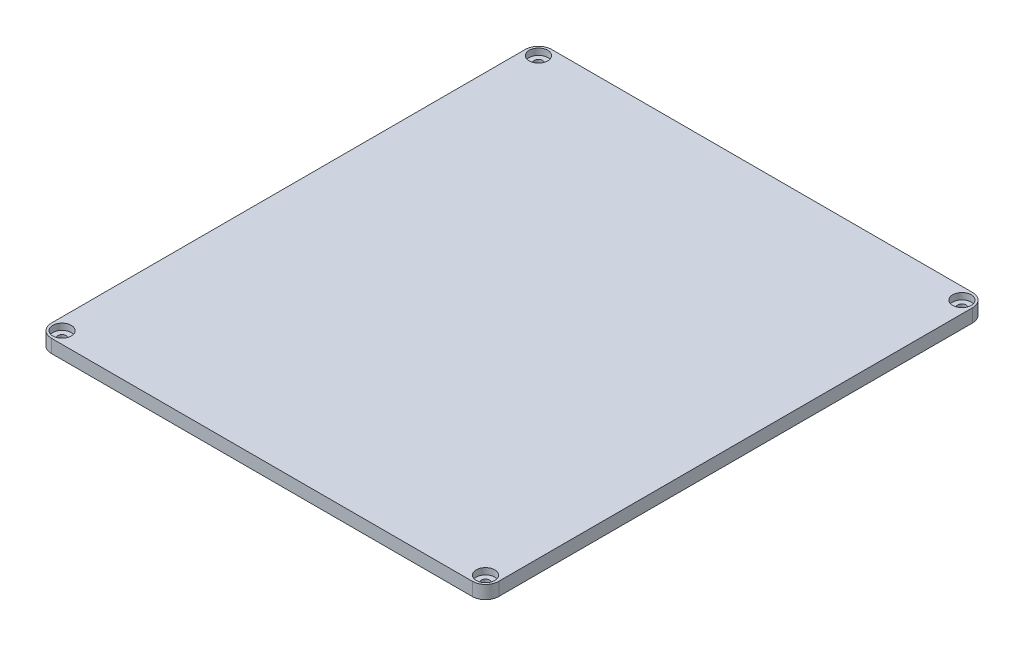
SolidWorks part; units mm, degrees
ref_plane "Alzado" through (0, 0, 0) normal (0, 0, 1) x (1, 0, 0)
ref_plane "Planta" through (0, 0, 0) normal (0, 1, 0) x (1, 0, 0)
ref_plane "Vista lateral" through (0, 0, 0) normal (1, 0, 0) x (0, 0, -1)
sketch "Croquis1" plane through (0, 0, 0) normal (0, 1, 0) x (1, 0, 0)
  line L1 (-79.5, -94.5) -> (79.5, -94.5)
  line L2 (-84.5, -89.5) -> (-84.5, 89.5)
  line L3 (-79.5, 94.5) -> (79.5, 94.5)
  line L4 (84.5, -89.5) -> (84.5, 89.5)
  line L5 (-84.5, -94.5) -> (84.5, 94.5) construction
  line L6 (-84.5, 94.5) -> (84.5, -94.5) construction
  line L7 (-85, -95) -> (85, -95) construction
  line L8 (-85, -95) -> (-85, 95) construction
  line L9 (-85, 95) -> (85, 95) construction
  line L10 (85, -95) -> (85, 95) construction
  line L11 (-85, -95) -> (85, 95) construction
  line L12 (-85, 95) -> (85, -95) construction
  arc A0 (-79.5, -94.5) -> (-84.5, -89.5) centre (-79.5, -89.5) cw
  arc A1 (79.5, -94.5) -> (84.5, -89.5) centre (79.5, -89.5) ccw
  arc A2 (79.5, 94.5) -> (84.5, 89.5) centre (79.5, 89.5) cw
  arc A3 (-84.5, 89.5) -> (-79.5, 94.5) centre (-79.5, 89.5) cw
  point P0 (0, 0)
  point P6 (0, 0)
  dimension "D5" = 5
  dimension "D1" = 189
  dimension "D2" = 169
  dimension "D3" = 170
  dimension "D4" = 190
extrude "Saliente-Extruir2" add sketch "Croquis1" along normal blind 5
hole_wizard "Refrentado para tornillo con cabeza troncocónica de M31" positions "Croquis4" profile "Croquis5" counterbore size "M3" standard "Ansi Metric" end condition through all
sketch "Croquis4" plane through (0, 5, 0) normal (0, 1, 0) x (1, 0, 0)
  line L2 (-85, -95) -> (85, -95)
  line L3 (-85, -95) -> (-85, 95)
  line L4 (-85, 95) -> (85, 95)
  line L5 (85, -95) -> (85, 95)
  line L6 (-85, -95) -> (85, 95) construction
  line L7 (-85, 95) -> (85, -95) construction
  line L8 (0, 95) -> (0, -95) construction
  line L10 (-85, 0) -> (85, 0) construction
  point P0 (80, 90)
  point P114 (80, -90)
  point P115 (-80, -90)
  point P116 (-80, 90)
  dimension "D1" = 5
  dimension "D2" = 170
  dimension "D3" = 190
  dimension "D4" = 5
sketch "Croquis5" plane through (80, 5, -90) normal (1, 0, 0) x (0, 0, 1)
  line L0 (0, 0) -> (0, 5)
  line L1 (0, 5) -> (1.6, 5)
  line L3 (1.6, 5) -> (1.6, 2.4)
  line L4 (3.5, 2.4) -> (1.6, 2.4)
  line L5 (3.5, 2.4) -> (3.5, -2)
  line L6 (3.5, -2) -> (1.5, 0)
  line L7 (1.5, 0) -> (0, 0)
  line L8 (-3.5, -2) -> (-1.5, 0) construction
  line L11 (0, -6.35) -> (0, 107.95) construction
  dimension "Diámetro de taladro hasta el siguiente" = 3.2
  dimension "Profundidad de taladro hasta el siguiente" = 5
  dimension "Diámetro de refrentado" = 7
  dimension "Profundidad de refrentado" = 2.4
  dimension "Diámetro de avellanado cercano" = 7
  dimension "Ángulo de avellanado cercano" = 90
sketch "Croquis6" plane through (0, 0, 0) normal (0, -1, 0) x (1, 0, 0)
  line L0 (-81, 84) -> (-74, 91)
  line L1 (-74, -91) -> (74, -91)
  line L2 (-81, -84) -> (-81, 84)
  line L3 (-74, 91) -> (74, 91)
  line L4 (81, -84) -> (81, 84)
  line L5 (-81, -91) -> (81, 91) construction
  line L6 (-81, 91) -> (81, -91) construction
  line L7 (74, 91) -> (81, 84)
  line L8 (74, -91) -> (81, -84)
  line L9 (-81, -84) -> (-74, -91)
  point P0 (0, 0)
  dimension "D1" = 162
  dimension "D2" = 182
extrude "Cortar-Extruir1" cut sketch "Croquis6" against normal blind 2
sketch "Croquis8" plane through (0, 2, 0) normal (0, -1, 0) x (1, 0, 0)
  line L0 (-81, 84) -> (-81, -84) construction
  line L6 (74, 91) -> (-74, 91) construction
  line L7 (-81, 84) -> (-71, 84)
  line L8 (-81, 84) -> (-81, 74)
  line L9 (-81, 74) -> (-71, 74)
  line L10 (-71, 84) -> (-71, 74)
  line L11 (0, 91) -> (0, -91) construction
  line L12 (-74, -91) -> (74, -91) construction
  line L13 (-81, 0) -> (81, 0) construction
  line L14 (81, -84) -> (81, 84) construction
  line L15 (81, 74) -> (71, 74)
  line L16 (71, 84) -> (71, 74)
  line L17 (81, 84) -> (71, 84)
  line L18 (81, 84) -> (81, 74)
  line L19 (-81, -74) -> (-71, -74)
  line L20 (-71, -84) -> (-71, -74)
  line L21 (-81, -84) -> (-71, -84)
  line L22 (-81, -84) -> (-81, -74)
  line L23 (81, -84) -> (81, -74)
  line L24 (81, -84) -> (71, -84)
  line L25 (71, -84) -> (71, -74)
  line L26 (81, -74) -> (71, -74)
  dimension "D5" = 0
  dimension "D6" = 7
  dimension "D7" = 10
  dimension "D8" = 10
extrude "Saliente-Extruir7" add sketch "Croquis8" along normal blind 5
hole_wizard "Taladro de margen para M31" positions "Croquis19" profile "Croquis20" hole size "M3" standard "Ansi Metric"
sketch "Croquis19" plane through (0, -3, 0) normal (0, -1, 0) x (-1, 0, 0)
  line L0 (-71, 84) -> (-81, 84) construction
  line L1 (-81, 84) -> (-81, 74) construction
  line L2 (0, 91) -> (0, -91) construction
  line L3 (74, 91) -> (-74, 91) construction
  line L4 (-74, -91) -> (74, -91) construction
  line L6 (-81, 0) -> (81, 0) construction
  line L7 (-81, 74) -> (-81, -74) construction
  line L8 (81, -74) -> (81, 74) construction
  point P0 (-76, 79)
  point P23 (76, 79)
  point P24 (76, -79)
  point P25 (-76, -79)
  dimension "D1" = 5
  dimension "D2" = 5
sketch "Croquis20" plane through (76, -3, -79) normal (1, 0, 0) x (0, 0, -1)
  line L0 (0, 0) -> (0, 5.9614)
  line L1 (0, 5.9614) -> (1.6, 5)
  line L2 (1.6, 5) -> (1.6, 0)
  line L5 (1.6, 0) -> (0, 0)
  line L10 (0, 5.9614) -> (-1.6, 5) construction
  line L11 (0, -6.35) -> (0, 107.95) construction
  dimension "Diámetro de taladro" = 3.2
  dimension "Profundidad de taladro" = 5
  dimension "Ángulo de perforador" = 118
